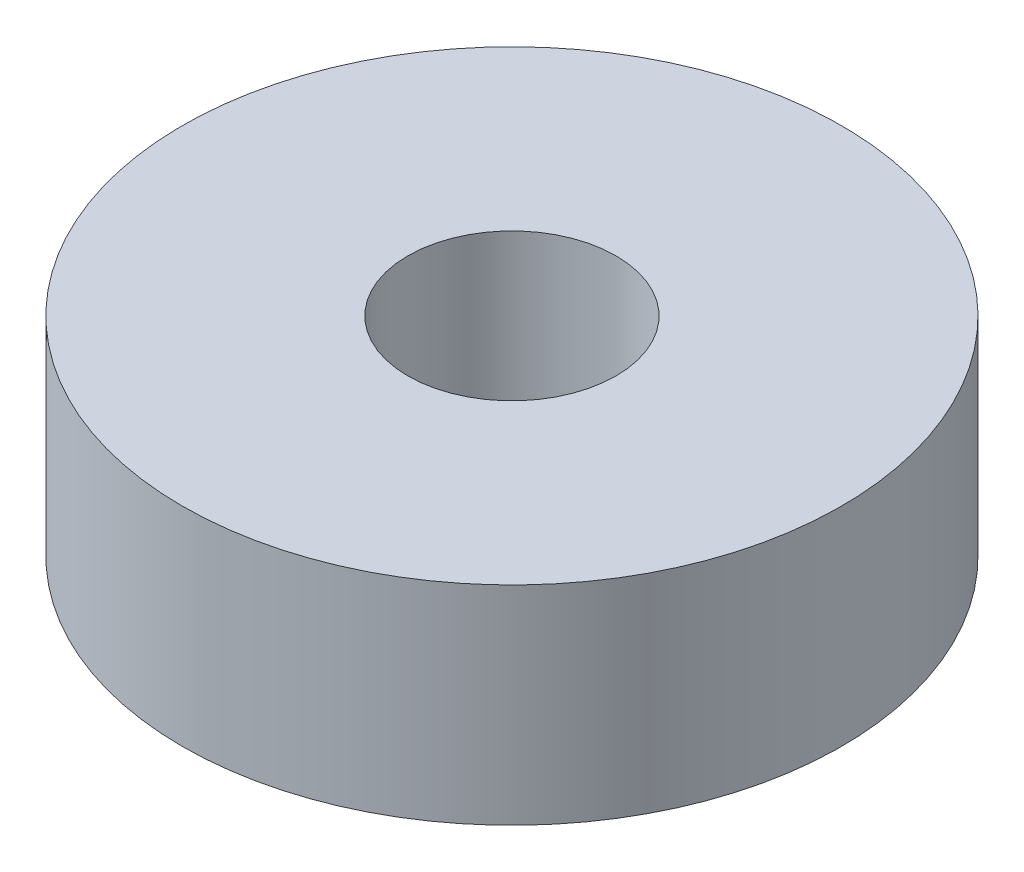
SolidWorks part; units mm, degrees
material "Alloy Steel"
ref_plane "Front Plane" through (0, 0, 0) normal (0, 0, 1) x (1, 0, 0)
ref_plane "Top Plane" through (0, 0, 0) normal (0, 1, 0) x (1, 0, 0)
ref_plane "Right Plane" through (0, 0, 0) normal (1, 0, 0) x (0, 0, -1)
sketch "Sketch1" plane through (0, 0, 0) normal (0, 1, 0) x (1, 0, 0)
  circle A0 centre (0, 0) radius 9.5
  circle A1 centre (0, 0) radius 3
  dimension "D1" = 6
  dimension "D2" = 19
extrude "Boss-Extrude1" add sketch "Sketch1" along normal blind 6
